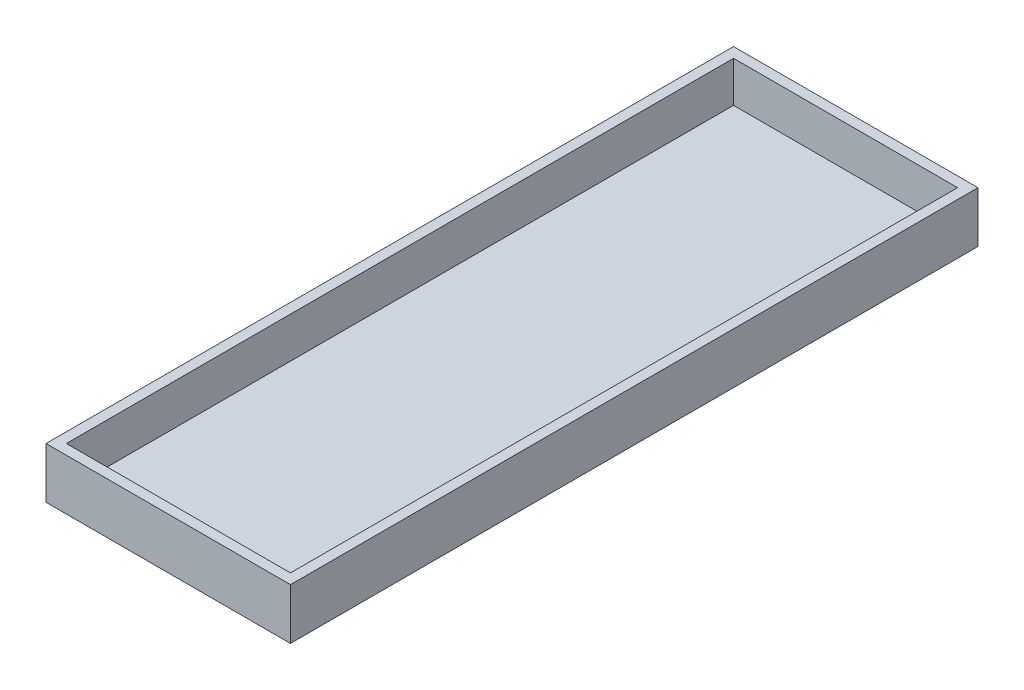
SolidWorks part; units mm, degrees
ref_plane "Front Plane" through (0, 0, 0) normal (0, 0, 1) x (1, 0, 0)
ref_plane "Top Plane" through (0, 0, 0) normal (0, 1, 0) x (1, 0, 0)
ref_plane "Right Plane" through (0, 0, 0) normal (1, 0, 0) x (0, 0, -1)
sketch "Sketch3" plane through (0, 0, 0) normal (0, 0, 1) x (1, 0, 0)
  line L1 (0, 0) -> (96, 0)
  line L2 (0, 0) -> (0, 20)
  line L3 (0, 20) -> (96, 20)
  line L4 (96, 0) -> (96, 20)
  dimension "D1" = 20
  dimension "D2" = 96
extrude "Boss-Extrude1" add sketch "Sketch3" against normal blind 270
shell "Shell1" thickness 4
